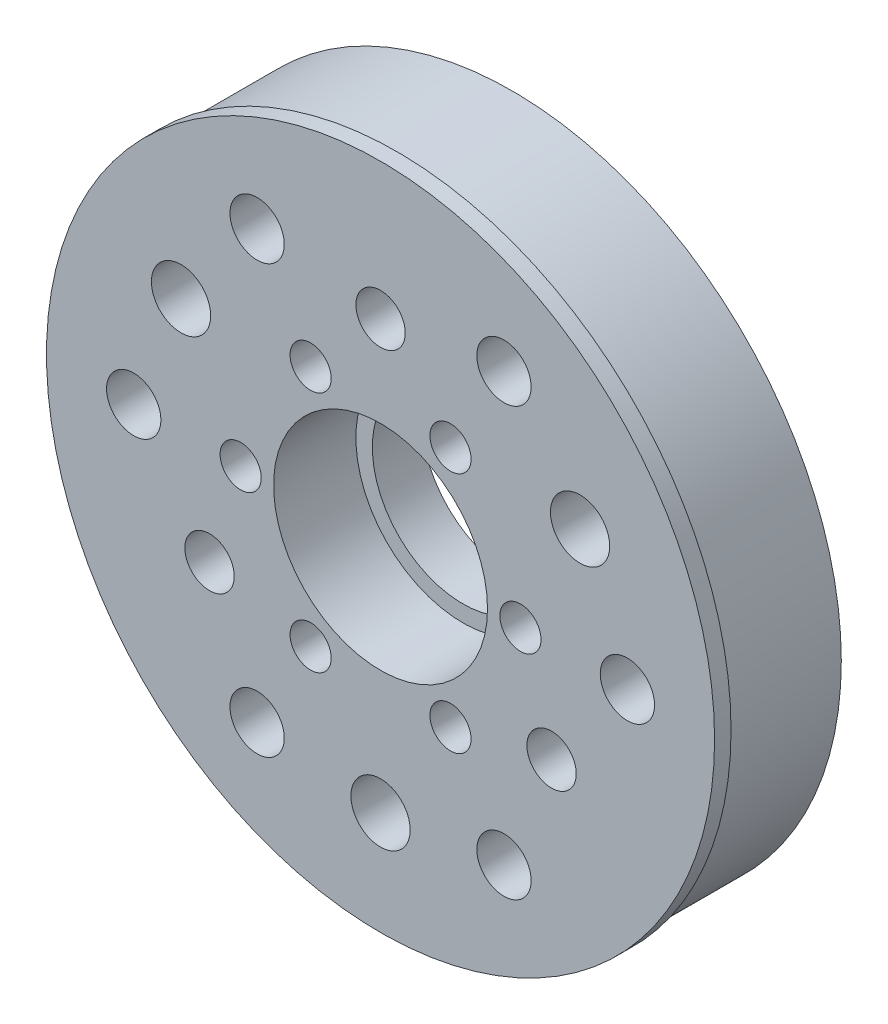
SolidWorks part; units mm, degrees
ref_plane "正面" through (0, 0, 0) normal (0, 0, 1) x (1, 0, 0)
ref_plane "平面" through (0, 0, 0) normal (0, 1, 0) x (1, 0, 0)
ref_plane "右側面" through (0, 0, 0) normal (1, 0, 0) x (0, 0, -1)
sketch "ｽｹｯﾁ1" plane through (0, 0, 0) normal (0, 0, 1) x (1, 0, 0)
  circle A0 centre (0, 0) radius 20
  dimension "D1" = 40
extrude "ﾎﾞｽ - 押し出し1" add sketch "ｽｹｯﾁ1" along normal blind 7 contours A0
sketch "ｽｹｯﾁ2" plane through (0, 0, 7) normal (0, 0, 1) x (1, 0, 0)
  circle A0 centre (0, 0) radius 20.3
  circle A1 centre (0, 0) radius 20 construction
  dimension "D1" = 0.3
extrude "ﾎﾞｽ - 押し出し2" add sketch "ｽｹｯﾁ2" along normal blind 1
sketch "ｽｹｯﾁ3" plane through (0, 0, 8) normal (0, 0, 1) x (1, 0, 0)
  circle A0 centre (0, 0) radius 6.5
  dimension "D1" = 13
extrude "ｶｯﾄ - 押し出し1" cut sketch "ｽｹｯﾁ3" against normal blind 5
sketch "ｽｹｯﾁ4" plane through (0, 0, 3) normal (0, 0, 1) x (1, 0, 0)
  circle A0 centre (0, 0) radius 5.5
  circle A1 centre (0, 0) radius 6.5 construction
  dimension "D1" = 1
extrude "ｶｯﾄ - 押し出し2" cut sketch "ｽｹｯﾁ4" against normal through all
sketch "ｽｹｯﾁ5" plane through (0, 0, 8) normal (0, 0, 1) x (1, 0, 0)
  circle A0 centre (0, 12) radius 1.5
  dimension "D1" = 12
  dimension "D2" = 3
extrude "ｶｯﾄ - 押し出し3" cut sketch "ｽｹｯﾁ5" against normal through all and the other way through all
pattern_circular "円形ﾊﾟﾀｰﾝ1" count 3 over 360 about axis through (0, 0, 0) along (0, 0, 1) of "ｶｯﾄ - 押し出し3"
hole_wizard "M3 平皿頭ねじ用皿穴1" positions "ｽｹｯﾁ6" profile "ｽｹｯﾁ7" countersink size "M3" standard "JIS" end condition through all
sketch "ｽｹｯﾁ6" plane through (0, 0, 0) normal (0, 0, -1) x (-1, 0, 0)
  point P0 (0, -14)
  dimension "D1" = 14
sketch "ｽｹｯﾁ7" plane through (0, -14, 0) normal (1, 0, 0) x (0, 1, 0)
  line L0 (0, 0) -> (0, 8)
  line L1 (0, 8) -> (1.8, 8)
  line L2 (1.8, 8) -> (1.8, 1.35)
  line L3 (1.8, 1.35) -> (3.15, 0)
  line L5 (3.15, 0) -> (0, 0)
  line L6 (-1.8, 1.35) -> (-3.15, 0) construction
  line L11 (0, -6.35) -> (0, 107.95) construction
  dimension "通し穴の直径" = 3.6
  dimension "通し穴の深さ" = 8
  dimension "表面の皿穴の直径" = 6.3
  dimension "表面の皿穴の角度" = 90
pattern_circular "円形ﾊﾟﾀｰﾝ2" count 3 over 360 about axis through (0, 0, 0) along (0, 0, 1) of "M3 平皿頭ねじ用皿穴1"
hole_wizard "M4x0.7 ねじ穴1" positions "ｽｹｯﾁ8" profile "ｽｹｯﾁ9" tap size "M4x0.7" standard "JIS" end condition through all
sketch "ｽｹｯﾁ8" plane through (0, 0, 0) normal (0, 0, -1) x (-1, 0, 0)
  point P0 (15, 0)
  dimension "D1" = 15
sketch "ｽｹｯﾁ9" plane through (-15, 0, 0) normal (1, 0, 0) x (0, 1, 0)
  line L0 (0, 0) -> (0, 8)
  line L1 (0, 8) -> (1.65, 8)
  line L2 (1.65, 8) -> (1.65, 0)
  line L5 (1.65, 0) -> (0, 0)
  line L11 (0, -6.35) -> (0, 107.95) construction
  dimension "ねじ山の主要直径" = 3.3
  dimension "次ｻｰﾌｪｽまでのねじ下穴ﾄﾞﾘﾙの深さ" = 8
hole_wizard "M3x0.5 ねじ穴1" positions "ｽｹｯﾁ10" profile "ｽｹｯﾁ11" tap size "M3x0.5" standard "JIS" end condition through all
sketch "ｽｹｯﾁ10" plane through (0, 0, 0) normal (0, 0, -1) x (-1, 0, 0)
  point P0 (8.5, 0)
  dimension "D1" = 8.5
sketch "ｽｹｯﾁ11" plane through (-8.5, 0, 0) normal (1, 0, 0) x (0, 1, 0)
  line L0 (0, 0) -> (0, 8)
  line L1 (0, 8) -> (1.25, 8)
  line L2 (1.25, 8) -> (1.25, 0)
  line L5 (1.25, 0) -> (0, 0)
  line L11 (0, -6.35) -> (0, 107.95) construction
  dimension "ねじ山の主要直径" = 2.5
  dimension "次ｻｰﾌｪｽまでのねじ下穴ﾄﾞﾘﾙの深さ" = 8
pattern_circular "円形ﾊﾟﾀｰﾝ3" count 6 over 360 about axis through (0, 0, 0) along (0, 0, 1) of "M4x0.7 ねじ穴1", "M3x0.5 ねじ穴1"
